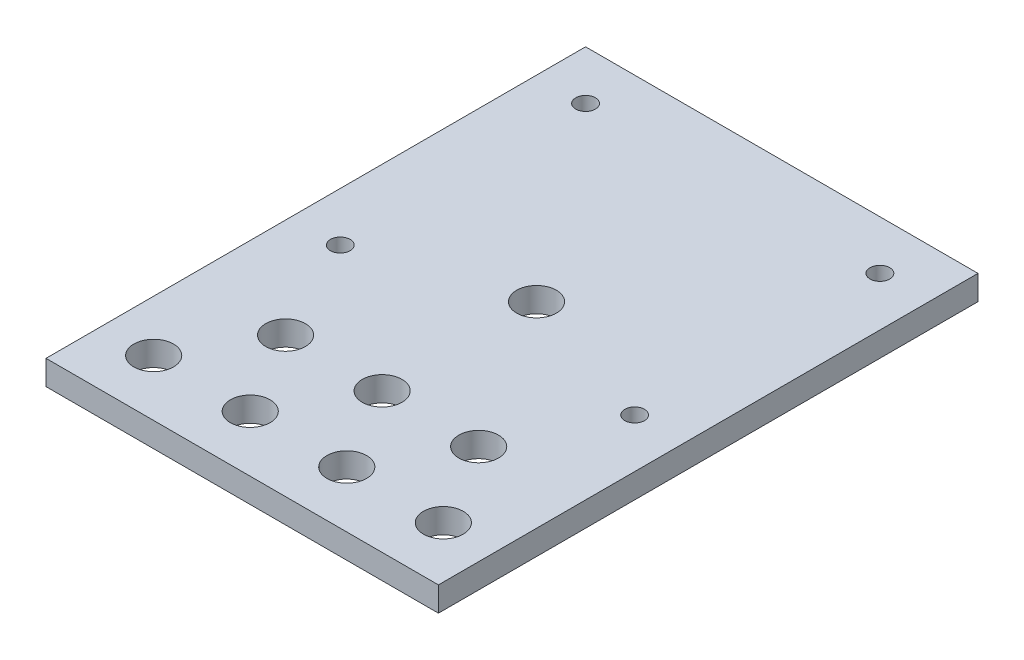
SolidWorks part; units mm, degrees
material "Acrylic (Medium-high impact)"
ref_plane "Front Plane" through (0, 0, 0) normal (0, 0, 1) x (1, 0, 0)
ref_plane "Top Plane" through (0, 0, 0) normal (0, 1, 0) x (1, 0, 0)
ref_plane "Right Plane" through (0, 0, 0) normal (1, 0, 0) x (0, 0, -1)
sketch "Sketch1" plane through (0, 0, 0) normal (0, 1, 0) x (1, 0, 0)
  line L1 (0, 0) -> (101.6, 0)
  line L2 (0, 0) -> (0, 139.7)
  line L3 (0, 139.7) -> (101.6, 139.7)
  line L4 (101.6, 0) -> (101.6, 139.7)
  dimension "D1" = 101.6
  dimension "D2" = 139.7
extrude "Boss-Extrude1" add sketch "Sketch1" along normal blind 6.35
sketch "Sketch2" plane through (0, 6.35, 0) normal (0, 1, 0) x (1, 0, 0)
  line L0 (88.3, 14.5747) -> (63.3, 14.5747) construction
  line L1 (38.3, 14.5747) -> (63.3, 14.5747) construction
  line L2 (0, 139.7) -> (0, 0) construction
  line L3 (50.8, 36.2253) -> (50.8, 14.5747) construction
  line L4 (0, 0) -> (101.6, 0) construction
  line L5 (101.6, 139.7) -> (0, 139.7) construction
  line L6 (101.6, 0) -> (101.6, 139.7) construction
  circle A0 centre (13.3, 14.5747) radius 5.1435
  circle A1 centre (38.3, 14.5747) radius 5.1435
  circle A2 centre (63.3, 14.5747) radius 5.1435
  circle A3 centre (88.3, 14.5747) radius 5.1435
  circle A4 centre (75.8, 36.2253) radius 5.1435
  circle A6 centre (50.8, 36.2253) radius 5.1435
  circle A7 centre (25.8, 36.2253) radius 5.1435
  circle A8 centre (12.7, 63.5) radius 2.55
  circle A9 centre (12.7, 127) radius 2.55
  circle A10 centre (88.9, 63.5) radius 2.55
  circle A11 centre (88.9, 127) radius 2.55
  circle A12 centre (50.8, 76.2) radius 5.1435
  point P2 (50.8, 14.5747)
  point P13 (75.8, 14.5747)
  point P14 (50.8, 25.4)
  dimension "D1" = 10.287
  dimension "D4" = 10.287
  dimension "D6" = 25.4
  dimension "D8" = 5.1
  dimension "D11" = 5.1
  dimension "D15" = 5.1
  dimension "D18" = 5.1
  dimension "D21" = 10.287
  dimension "D3" = 50.8
  dimension "D5" = 21.6506
  dimension "D9" = 63.5
  dimension "D10" = 12.7
  dimension "D12" = 12.7
  dimension "D13" = 12.7
  dimension "D14" = 25
  dimension "D16" = 12.7
  dimension "D17" = 63.5
  dimension "D19" = 12.7
  dimension "D20" = 12.7
  dimension "D22" = 12.7
  dimension "D2" = 4
  dimension "D7" = 3
extrude "Cut-Extrude1" cut sketch "Sketch2" against normal through all
